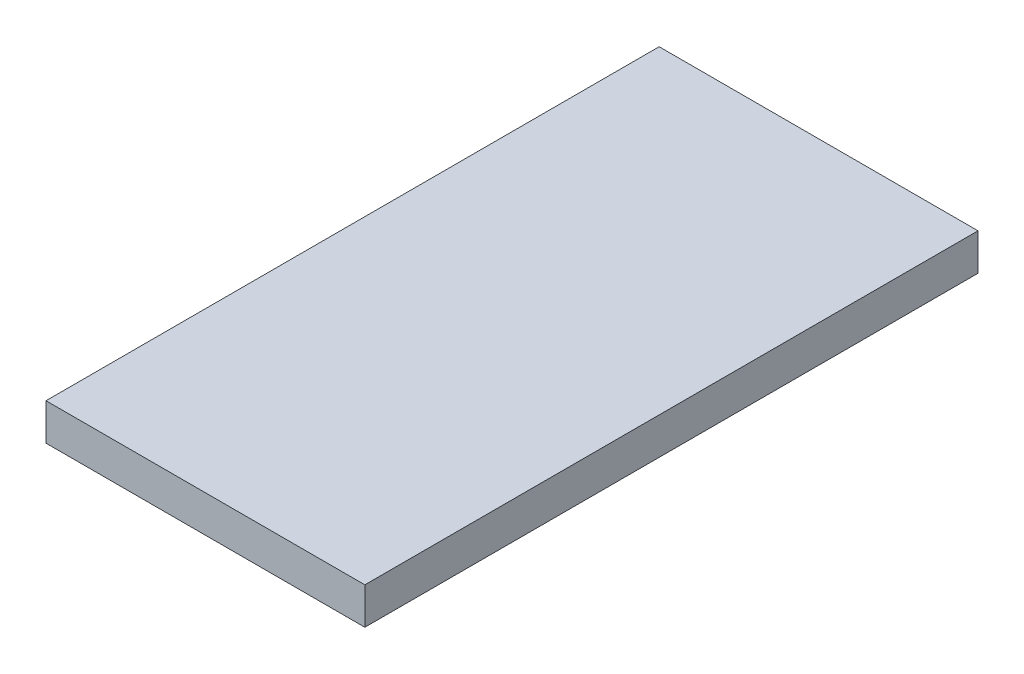
SolidWorks part; units mm, degrees
ref_plane "Alzado" through (0, 0, 0) normal (0, 0, 1) x (1, 0, 0)
ref_plane "Planta" through (0, 0, 0) normal (0, 1, 0) x (1, 0, 0)
ref_plane "Vista lateral" through (0, 0, 0) normal (1, 0, 0) x (0, 0, -1)
sketch "Croquis1" plane through (0, 0, 0) normal (0, 1, 0) x (1, 0, 0)
  line L1 (0, 0) -> (26, 0)
  line L2 (0, 0) -> (0, 50)
  line L3 (0, 50) -> (26, 50)
  line L4 (26, 0) -> (26, 50)
  dimension "D1" = 50
  dimension "D2" = 26
extrude "Saliente-Extruir1" add sketch "Croquis1" along normal blind 3
